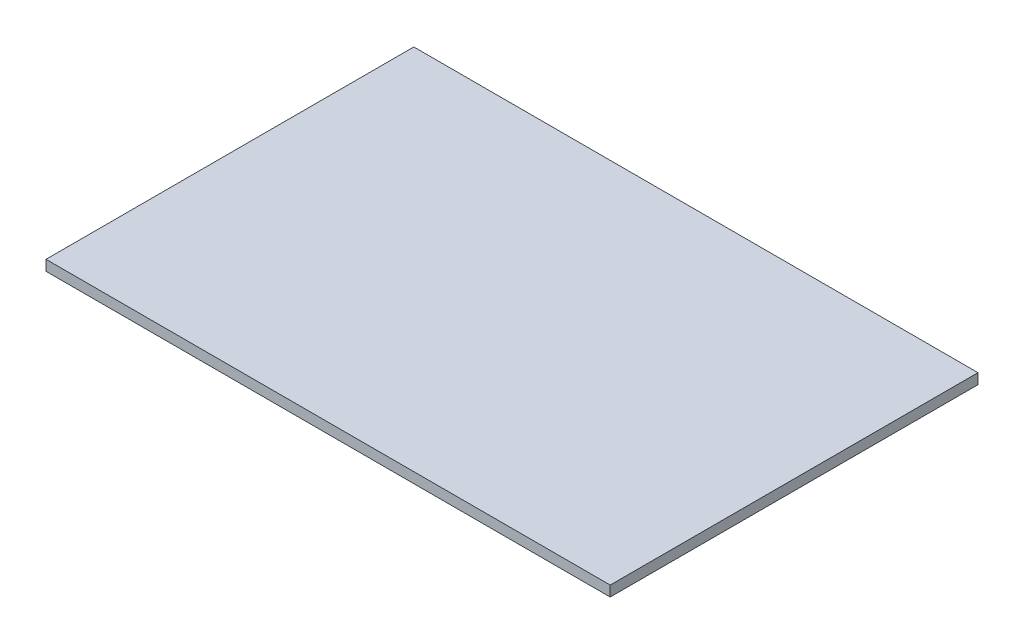
SolidWorks part; units mm, degrees
material "Placa de circuito impreso"
ref_plane "Alzado" through (0, 0, 0) normal (0, 0, 1) x (1, 0, 0)
ref_plane "Planta" through (0, 0, 0) normal (0, 1, 0) x (1, 0, 0)
ref_plane "Vista lateral" through (0, 0, 0) normal (1, 0, 0) x (0, 0, -1)
sketch "Croquis1" plane through (0, 0, 0) normal (0, 1, 0) x (1, 0, 0)
  line L1 (-40.65, -26.5) -> (40.65, -26.5)
  line L2 (-40.65, -26.5) -> (-40.65, 26.5)
  line L3 (-40.65, 26.5) -> (40.65, 26.5)
  line L4 (40.65, -26.5) -> (40.65, 26.5)
  line L5 (-40.65, -26.5) -> (40.65, 26.5) construction
  line L6 (-40.65, 26.5) -> (40.65, -26.5) construction
  point P0 (0, 0)
  dimension "D1" = 81.3
  dimension "D2" = 53
extrude "Saliente-Extruir1" add sketch "Croquis1" along normal blind 1.5
